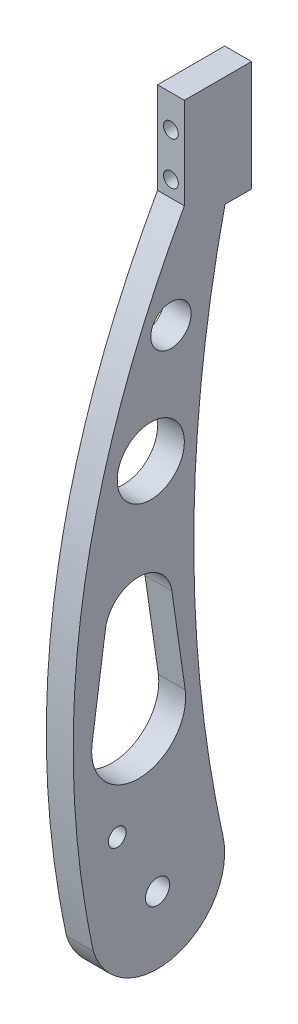
SolidWorks part; units mm, degrees
ref_plane "Front Plane" through (0, 0, 0) normal (0, 0, 1) x (1, 0, 0)
ref_plane "Top Plane" through (0, 0, 0) normal (0, 1, 0) x (1, 0, 0)
ref_plane "Right Plane" through (0, 0, 0) normal (1, 0, 0) x (0, 0, -1)
sketch "Sketch1" plane through (0, 0, 0) normal (1, 0, 0) x (0, 0, -1)
  line L0 (25, 0) -> (25, 250) construction
  line L1 (-24.3389, 59.8667) -> (-19.3902, 94.1524)
  line L2 (10, 215.9797) -> (10, 250)
  line L4 (5.3533, 94.1524) -> (10.3021, 59.8667)
  line L5 (10, 250) -> (25, 250)
  line L6 (25.123, 208.8979) -> (35, 208.8979)
  line L7 (35, 208.8979) -> (35, 250)
  line L8 (35, 250) -> (25, 250)
  arc A0 (-23.9025, -7.3259) -> (24.3852, 5.5103) centre (0, 0) ccw
  arc A1 (-24.3389, 59.8667) -> (10.3021, 59.8667) centre (-7.0184, 57.3667) ccw
  arc A2 (24.3852, 5.5103) -> (25.123, 208.8979) centre (478.9447, 105.5565) cw
  arc A3 (5.3533, 94.1524) -> (-19.3902, 94.1524) centre (-7.0184, 92.3667) ccw
  circle A5 centre (5, 180) radius 7.5
  circle A6 centre (-2.5, 140) radius 12.5
  spline S0 degree 2 poles (-23.9025, -7.3259) (-48.9902, 110.1511) (10, 215.9797) knots 0 0 0 1 1 1
  dimension "D1" = 50
  dimension "D3" = 35
  dimension "D5" = 25
  dimension "D8" = 465.4391
  dimension "D12" = 15
  dimension "D15" = 25
  dimension "D6" = 64.0369
  dimension "D2" = 250
  dimension "D4" = 25
  dimension "D13" = 70
  dimension "D14" = 35
  dimension "D17" = 110
extrude "Boss-Extrude1" add sketch "Sketch1" along normal blind 10
sketch "Sketch2" plane through (0, 0, -35) normal (0, 0, -1) x (-1, 0, 0)
  line L0 (-10, 250) -> (0, 250) construction
  line L1 (-10, 230) -> (0, 230) construction
  point P0 (-4.9839, 222)
  point P1 (-4.9839, 238)
  dimension "D1" = 12
hole_wizard "M5 Clearance Hole2" positions "Sketch5" profile "Sketch6" hole size "M5" standard "BSI"
sketch "Sketch5" plane through (0, 0, -35) normal (0, 0, -1) x (-1, 0, 0)
  point P0 (-4.9839, 238)
  point P3 (-4.9839, 222)
sketch "Sketch6" plane through (4.9839, 238, -35) normal (1, 0, 0) x (0, 1, 0)
  line L0 (0, 0) -> (0, 31.6524)
  line L1 (0, 31.6524) -> (2.75, 30)
  line L2 (2.75, 30) -> (2.75, 0)
  line L5 (2.75, 0) -> (0, 0)
  line L10 (0, 31.6524) -> (-2.75, 30) construction
  line L11 (0, -6.35) -> (0, 107.95) construction
  dimension "Hole Dia." = 5.5
  dimension "Hole Depth" = 30
  dimension "Drill Angle" = 118
sketch "Sketch7" plane through (10, 0, 0) normal (1, 0, 0) x (0, 0, -1)
  line L0 (35, 208.8979) -> (35, 250) construction
  line L1 (25.123, 208.8979) -> (35, 208.8979) construction
  point P0 (0, -1.1021)
  point P5 (30.0615, 208.8979)
  dimension "D1" = 35
  dimension "D2" = 210
hole_wizard "M8 Clearance Hole1" positions "Sketch8" profile "Sketch9" hole size "M8" standard "BSI"
sketch "Sketch8" plane through (10, 0, 0) normal (1, 0, 0) x (0, 0, -1)
  point P0 (0, 0)
sketch "Sketch9" plane through (10, 0, 0) normal (0, 1, 0) x (0, 0, -1)
  line L0 (0, 0) -> (0, 32.7039)
  line L1 (0, 32.7039) -> (4.5, 30)
  line L2 (4.5, 30) -> (4.5, 0)
  line L5 (4.5, 0) -> (0, 0)
  line L10 (0, 32.7039) -> (-4.5, 30) construction
  line L11 (0, -6.35) -> (0, 107.95) construction
  dimension "Hole Dia." = 9
  dimension "Hole Depth" = 30
  dimension "Drill Angle" = 118
sketch "Sketch10" plane through (0, 0, 0) normal (-1, 0, 0) x (0, 0, 1)
  line L0 (-35, 250) -> (-10, 250) construction
  line L1 (-35, 208.8979) -> (-35, 250) construction
  point P0 (15, 25)
  dimension "D1" = 225
  dimension "D2" = 50
hole_wizard "M6 Clearance Hole1" positions "Sketch11" profile "Sketch12" hole size "M6" standard "BSI"
sketch "Sketch11" plane through (0, 0, 0) normal (-1, 0, 0) x (0, 0, 1)
  point P0 (15, 25)
sketch "Sketch12" plane through (0, 25, 15) normal (0, 1, 0) x (0, 0, 1)
  line L0 (0, 0) -> (0, 31.9828)
  line L1 (0, 31.9828) -> (3.3, 30)
  line L2 (3.3, 30) -> (3.3, 0)
  line L5 (3.3, 0) -> (0, 0)
  line L10 (0, 31.9828) -> (-3.3, 30) construction
  line L11 (0, -6.35) -> (0, 107.95) construction
  dimension "Hole Dia." = 6.6
  dimension "Hole Depth" = 30
  dimension "Drill Angle" = 118
